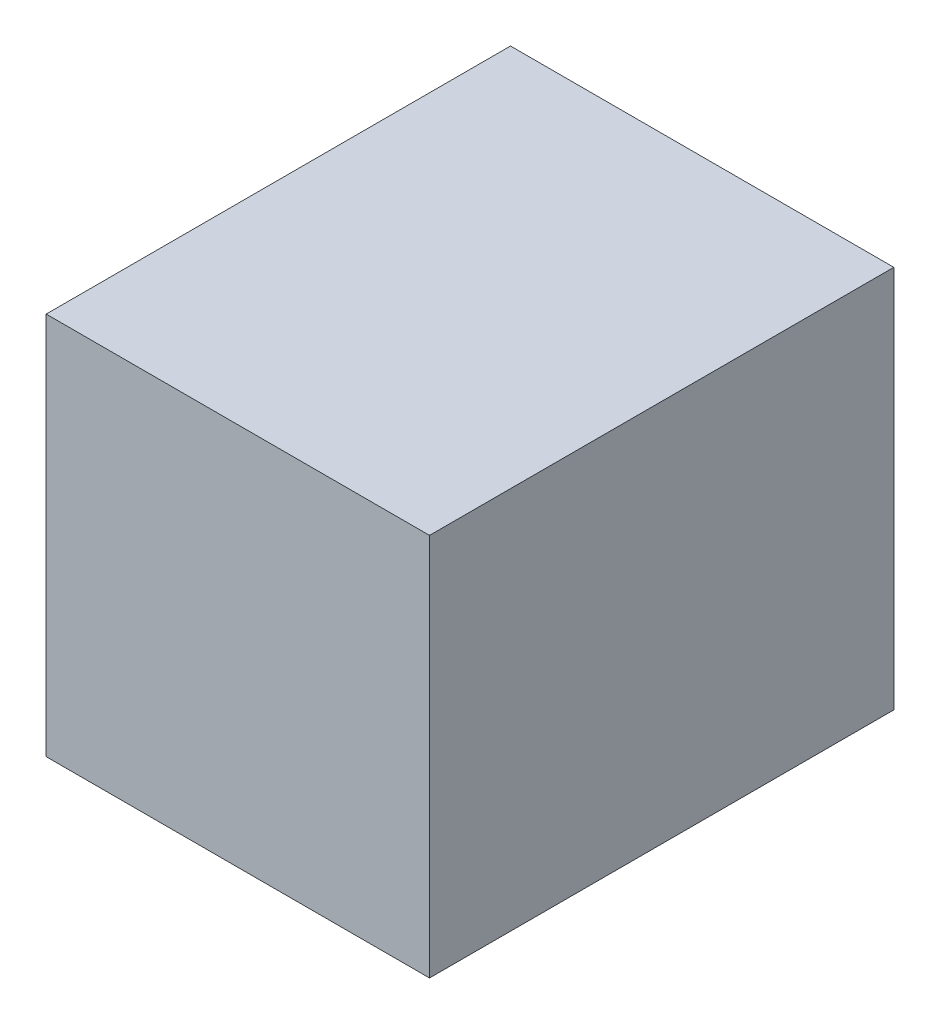
SolidWorks part; units mm, degrees
ref_plane "Front Plane" through (0, 0, 0) normal (0, 0, 1) x (1, 0, 0)
ref_plane "Top Plane" through (0, 0, 0) normal (0, 1, 0) x (1, 0, 0)
ref_plane "Right Plane" through (0, 0, 0) normal (1, 0, 0) x (0, 0, -1)
sketch "Sketch1" plane through (0, 0, 0) normal (0, 0, 1) x (1, 0, 0)
  line L1 (0, 0) -> (101.6, 0)
  line L2 (0, 0) -> (0, 101.6)
  line L3 (0, 101.6) -> (101.6, 101.6)
  line L4 (101.6, 0) -> (101.6, 101.6)
  dimension "D1" = 101.6
  dimension "D2" = 101.6
extrude "Boss-Extrude1" add sketch "Sketch1" along normal blind 123.063
hole_wizard "1/4 (0.25) Diameter Hole1" positions "Sketch3" profile "Sketch5" hole size "1/4" standard "ANSI Inch"
sketch "Sketch3" plane through (0, 0, 111.125) normal (0, 0, 1) x (1, 0, 0)
  line L0 (101.6, 0) -> (101.6, 101.6) construction
  line L1 (101.6, 101.6) -> (0, 101.6) construction
  point P0 (-25.4, 76.2)
  point P2 (76.2, 76.2)
  point P4 (76.2, -25.4)
  point P6 (-25.4, -25.4)
  dimension "D1" = 101.6
  dimension "D2" = 101.6
  dimension "D3" = 25.4
  dimension "D4" = 25.4
sketch "Sketch5" plane through (-25.4, 76.2, 111.125) normal (1, 0, 0) x (0, -1, 0)
  line L0 (0, 0) -> (0, 52.7077)
  line L1 (0, 52.7077) -> (3.175, 50.8)
  line L2 (3.175, 50.8) -> (3.175, 0.635)
  line L3 (3.175, 0.635) -> (3.81, 0)
  line L5 (3.81, 0) -> (0, 0)
  line L6 (-3.175, 0.635) -> (-3.81, 0) construction
  line L10 (0, 52.7077) -> (-3.175, 50.8) construction
  line L11 (0, -6.35) -> (0, 107.95) construction
  dimension "Hole Dia." = 6.35
  dimension "Hole Depth" = 50.8
  dimension "Near C'Sink Dia." = 7.62
  dimension "Near C'Sink Angle" = 90
  dimension "Drill Angle" = 118
